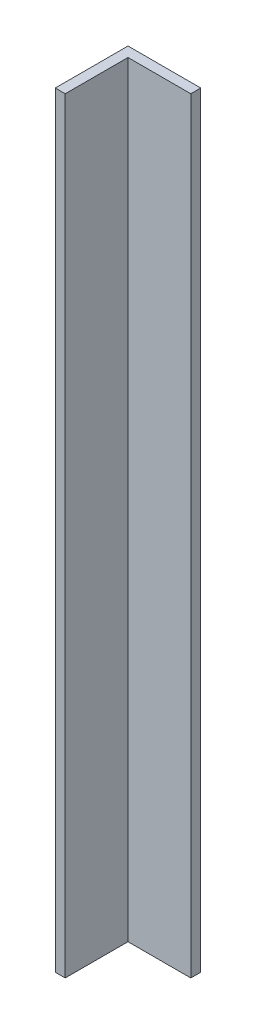
SolidWorks part; units mm, degrees
ref_plane "Front Plane" through (0, 0, 0) normal (0, 0, 1) x (1, 0, 0)
ref_plane "Top Plane" through (0, 0, 0) normal (0, 1, 0) x (1, 0, 0)
ref_plane "Right Plane" through (0, 0, 0) normal (1, 0, 0) x (0, 0, -1)
sketch "Sketch1" plane through (0, 0, 0) normal (0, 1, 0) x (1, 0, 0)
  line L0 (0, 0) -> (16.4, 0)
  line L1 (16.4, 0) -> (16.4, 2.6)
  line L2 (16.4, 2.6) -> (-2.6, 2.6)
  line L3 (-2.6, 2.6) -> (-2.6, -16.4)
  line L4 (-2.6, -16.4) -> (0, -16.4)
  line L5 (0, -16.4) -> (0, 0)
  dimension "D1" = 19
  dimension "D2" = 19
  dimension "D3" = 2.6
  dimension "D4" = 2.6
extrude "Boss-Extrude1" add sketch "Sketch1" along normal blind 200
